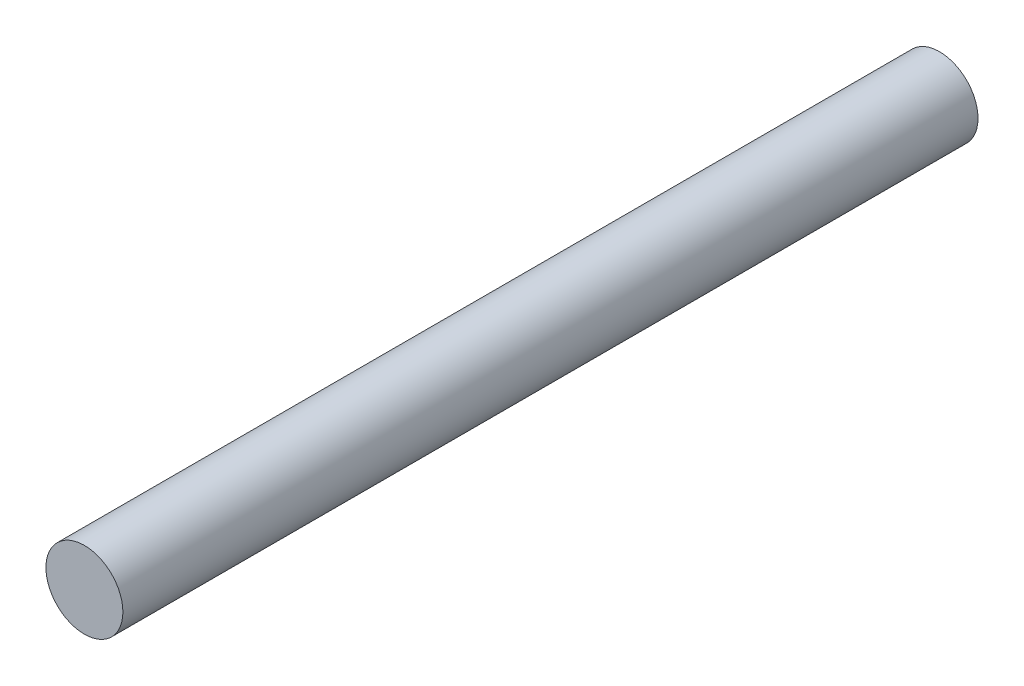
SolidWorks part; units mm, degrees
ref_plane "Front Plane" through (0, 0, 0) normal (0, 0, 1) x (1, 0, 0)
ref_plane "Top Plane" through (0, 0, 0) normal (0, 1, 0) x (1, 0, 0)
ref_plane "Right Plane" through (0, 0, 0) normal (1, 0, 0) x (0, 0, -1)
sketch "Sketch1" plane through (0, 0, 0) normal (0, 0, 1) x (1, 0, 0)
  circle A0 centre (0, 0) radius 9
  dimension "D1" = 18
extrude "Boss-Extrude1" add sketch "Sketch1" along normal blind 200
